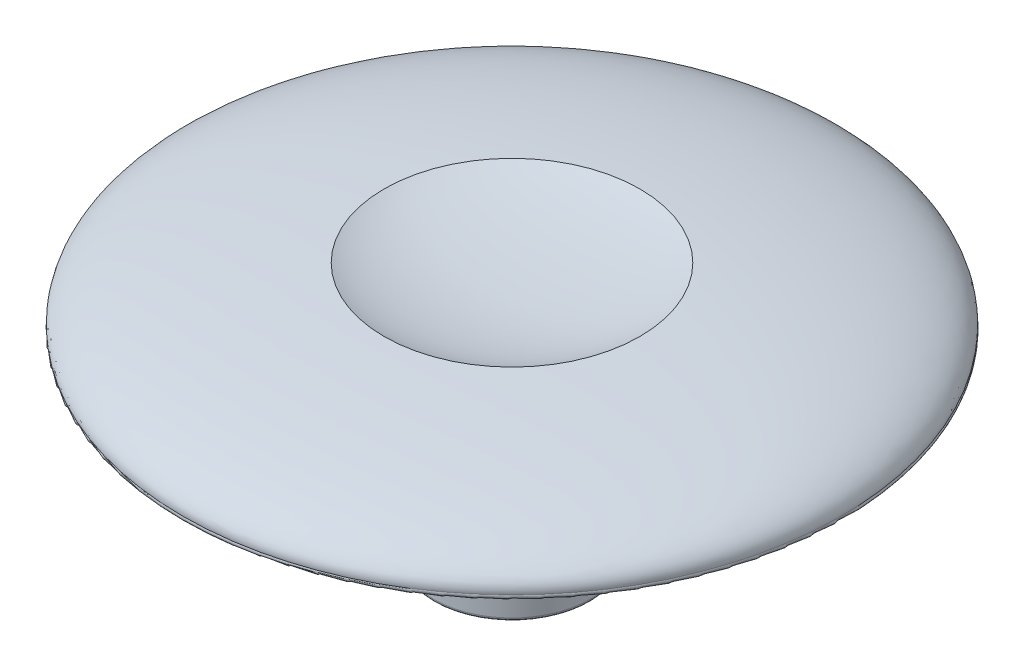
SolidWorks part; units mm, degrees
ref_plane "Front" through (0, 0, 0) normal (0, 0, 1) x (1, 0, 0)
ref_plane "Top" through (0, 0, 0) normal (0, 1, 0) x (1, 0, 0)
ref_plane "Right" through (0, 0, 0) normal (1, 0, 0) x (0, 0, -1)
sketch "Sketch1" plane through (0, 0, 0) normal (1, 0, 0) x (0, 0, -1)
  line L0 (0, 0) -> (0.7, 0)
  line L1 (0, 0.6284) -> (0, 0)
  line L2 (1.2, -0.1) -> (1.2, -2.95)
  line L3 (1.2, -0.1) -> (2, -0.1)
  line L4 (2, -0.1) -> (2, 0)
  line L5 (1.15, -3) -> (0.75, -3)
  line L6 (0.7, -2.95) -> (0.7, 0)
  line L7 (2, 0) -> (5, 0)
  arc A0 (5, 0) -> (5.0441, 0.0735) centre (5, 0.05) ccw
  arc A1 (0.75, -3) -> (0.7, -2.95) centre (0.75, -2.95) cw
  arc A2 (1.2, -2.95) -> (1.15, -3) centre (1.15, -2.95) cw
  ellipse E0 centre (0.0196, 1.2111) end of major axis (2.2668, 1.2111) minor radius 0.5828 (0, 0.6284) -> (1.9597, 0.917) ccw
  ellipse E2 centre (0, 0) end of major axis (5.0464, 0.1065) minor radius 0.9516 (5.0441, 0.0735) -> (1.9597, 0.917) ccw
  dimension "D1" = 0.05
  dimension "D2" = 0.5
  dimension "D3" = 1.2
  dimension "D4" = 0.8
  dimension "D5" = 5
revolve "Revolve1" add sketch "Sketch1" angle 360 about L1
